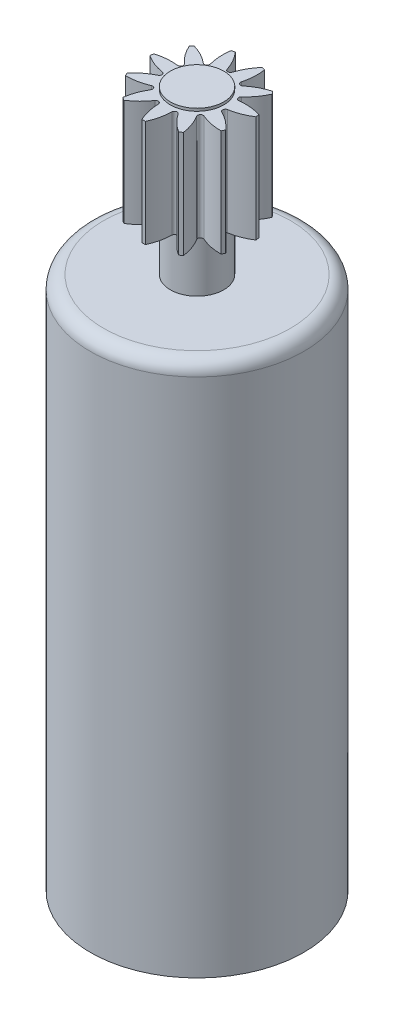
SolidWorks part; units mm, degrees
ref_plane "Front Plane" through (0, 0, 0) normal (0, 0, 1) x (1, 0, 0)
ref_plane "Top Plane" through (0, 0, 0) normal (0, 1, 0) x (1, 0, 0)
ref_plane "Right Plane" through (0, 0, 0) normal (1, 0, 0) x (0, 0, -1)
sketch "Sketch1" plane through (0, 0, 0) normal (0, 0, 1) x (1, 0, 0)
  line L0 (0, 0) -> (0, 26.1)
  line L1 (0, 26.1) -> (1, 26.1)
  line L2 (1, 26.1) -> (1, 26)
  line L3 (1, 26) -> (2, 26)
  line L4 (2, 26) -> (2, 22)
  line L5 (2, 22) -> (1, 22)
  line L6 (1, 22) -> (1, 20)
  line L7 (1, 20) -> (3.5, 20)
  line L8 (4, 19.5) -> (4, 0)
  line L9 (4, 0) -> (0, 0)
  arc A0 (3.5, 20) -> (4, 19.5) centre (3.5, 19.5) cw
  point P13 (4, 20)
  dimension "D9" = 0.5
  dimension "D1" = 26.1
  dimension "D2" = 1
  dimension "D3" = 0.1
  dimension "D4" = 4
  dimension "D5" = 1
  dimension "D6" = 3
  dimension "D7" = 4
  dimension "D8" = 2
revolve "Revolve1" add sketch "Sketch1" angle 360 about L0
sketch "Sketch2" plane through (0, 26, 0) normal (0, 1, 0) x (1, 0, 0)
  line L0 (0, 0) -> (0, 2) construction
  circle A0 centre (0, 0) radius 2 construction
  arc A1 (-0.5, 1.9365) -> (0.5, 1.9365) centre (0, 0) cw
  arc A2 (0.5, 1.9365) -> (0.0953, 1.2198) centre (2.002, 0.6158) ccw
  arc A3 (0.0953, 1.2198) -> (-0.0953, 1.2198) centre (0, 1.25) cw
  arc A4 (-0.5, 1.9365) -> (-0.0953, 1.2198) centre (-2.002, 0.6158) cw
  dimension "D2" = 2
  dimension "D3" = 0.1
  dimension "D1" = 1
  dimension "D4" = 0.75
extrude "Cut-Extrude1" cut sketch "Sketch2" against normal blind 5
pattern_circular "CirPattern1" count 11 over 360 about axis through (0, 0, 0) along (0, 1, 0) of "Cut-Extrude1"
